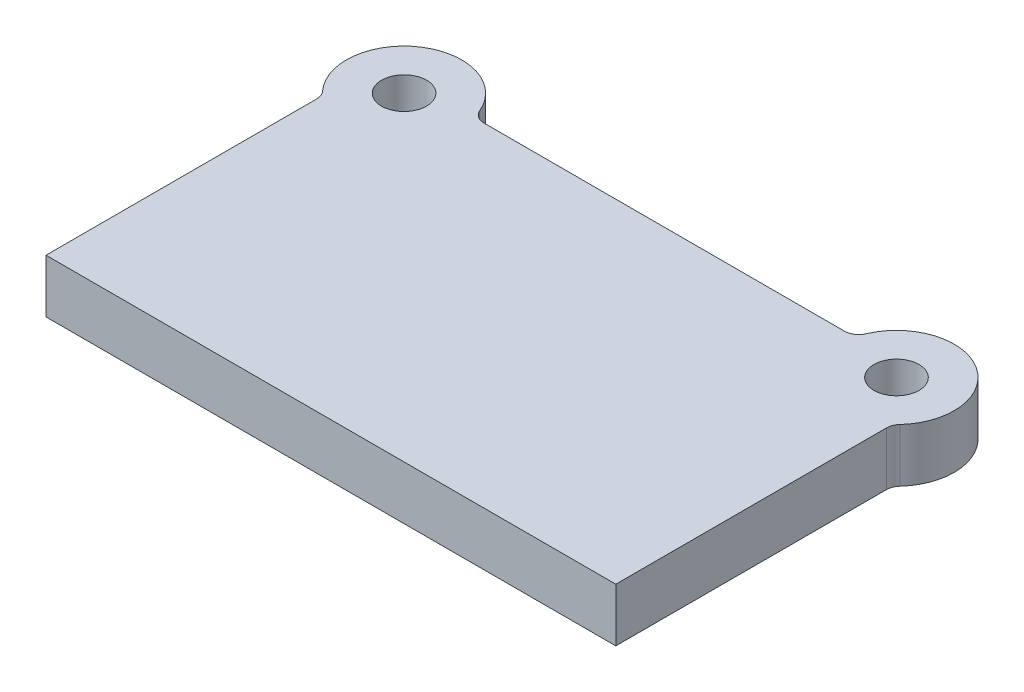
SolidWorks part; units mm, degrees
ref_plane "Front Plane" through (0, 0, 0) normal (0, 0, 1) x (1, 0, 0)
ref_plane "Top Plane" through (0, 0, 0) normal (0, 1, 0) x (1, 0, 0)
ref_plane "Right Plane" through (0, 0, 0) normal (1, 0, 0) x (0, 0, -1)
sketch "Sketch1" plane through (0, 0, 0) normal (0, 1, 0) x (1, 0, 0)
  line L0 (202.5, 0) -> (-202.5, 0)
  line L1 (-202.5, 0) -> (-202.5, 196.5903)
  line L2 (0, 0) -> (0, 237) construction
  line L3 (135.2382, 237) -> (-135.2382, 237)
  line L4 (202.5, 0) -> (202.5, 196.5903)
  arc A0 (-135.2382, 237) -> (-202.5, 196.5903) centre (-175, 227) ccw
  circle A1 centre (-175, 227) radius 16
  circle A2 centre (175, 227) radius 16
  arc A3 (135.2382, 237) -> (202.5, 196.5903) centre (175, 227) cw
  point P9 (-234.7863, 189.0248)
  point P10 (-162.9835, 254.5515)
  dimension "D3" = 82
  dimension "D4" = 32
  dimension "D1" = 227
  dimension "D2" = 237
  dimension "D5" = 405
  dimension "D6" = 350
extrude "Boss-Extrude1" add sketch "Sketch1" along normal blind 38
fillet "Fillet1" radius 10 4 edges at (-202.5, 19, -196.5903) (-135.2382, 19, -237) (135.2382, 19, -237) (202.5, 19, -196.5903)
